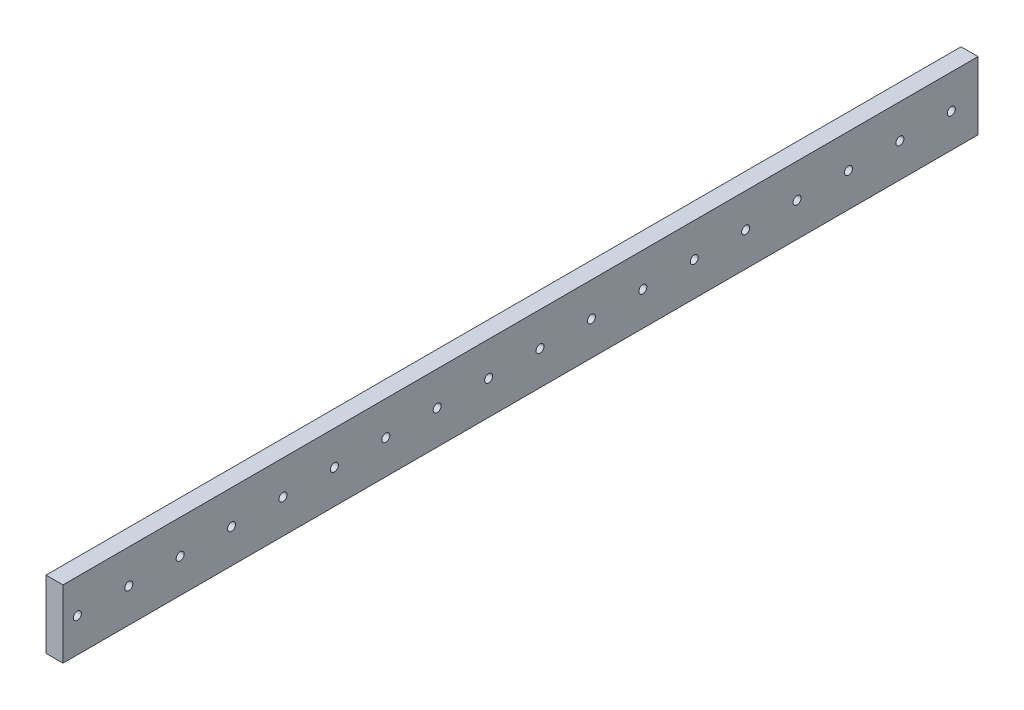
SolidWorks part; units mm, degrees
ref_plane "Alzado" through (0, 0, 0) normal (0, 0, 1) x (1, 0, 0)
ref_plane "Planta" through (0, 0, 0) normal (0, 1, 0) x (1, 0, 0)
ref_plane "Vista lateral" through (0, 0, 0) normal (1, 0, 0) x (0, 0, -1)
sketch "Croquis2" plane through (0, 0, 0) normal (0, 0, 1) x (1, 0, 0)
  line L1 (-6.35, -25.4) -> (6.35, -25.4)
  line L2 (-6.35, -25.4) -> (-6.35, 25.4)
  line L3 (-6.35, 25.4) -> (6.35, 25.4)
  line L4 (6.35, -25.4) -> (6.35, 25.4)
  line L5 (-6.35, -25.4) -> (6.35, 25.4) construction
  line L6 (-6.35, 25.4) -> (6.35, -25.4) construction
  point P0 (0, 0)
  dimension "D1" = 12.7
  dimension "D2" = 50.8
extrude "Saliente-Extruir1" add sketch "Croquis2" against normal blind 685.3
sketch "Croquis3" plane through (-6.35, 0, 0) normal (-1, 0, 0) x (0, 0, 1)
  line L0 (-685.3, 0) -> (-665.3, 0) construction
  line L1 (-685.3, 25.4) -> (-685.3, -25.4) construction
  circle A0 centre (-665.3, 0) radius 3
  circle A1 centre (-626.8, 0) radius 3
  circle A2 centre (-588.3, 0) radius 3
  circle A3 centre (-549.8, 0) radius 3
  circle A4 centre (-511.3, 0) radius 3
  circle A5 centre (-472.8, 0) radius 3
  circle A6 centre (-434.3, 0) radius 3
  circle A7 centre (-395.8, 0) radius 3
  circle A8 centre (-357.3, 0) radius 3
  circle A9 centre (-318.8, 0) radius 3
  circle A10 centre (-280.3, 0) radius 3
  circle A11 centre (-241.8, 0) radius 3
  circle A12 centre (-203.3, 0) radius 3
  circle A13 centre (-164.8, 0) radius 3
  circle A14 centre (-126.3, 0) radius 3
  circle A15 centre (-87.8, 0) radius 3
  circle A16 centre (-49.3, 0) radius 3
  circle A17 centre (-10.8, 0) radius 3
  dimension "D1" = 6
  dimension "D2" = 20
  dimension "D4" = 38.5
  dimension "D3" = 18
extrude "Cortar-Extruir1" cut sketch "Croquis3" against normal through all
